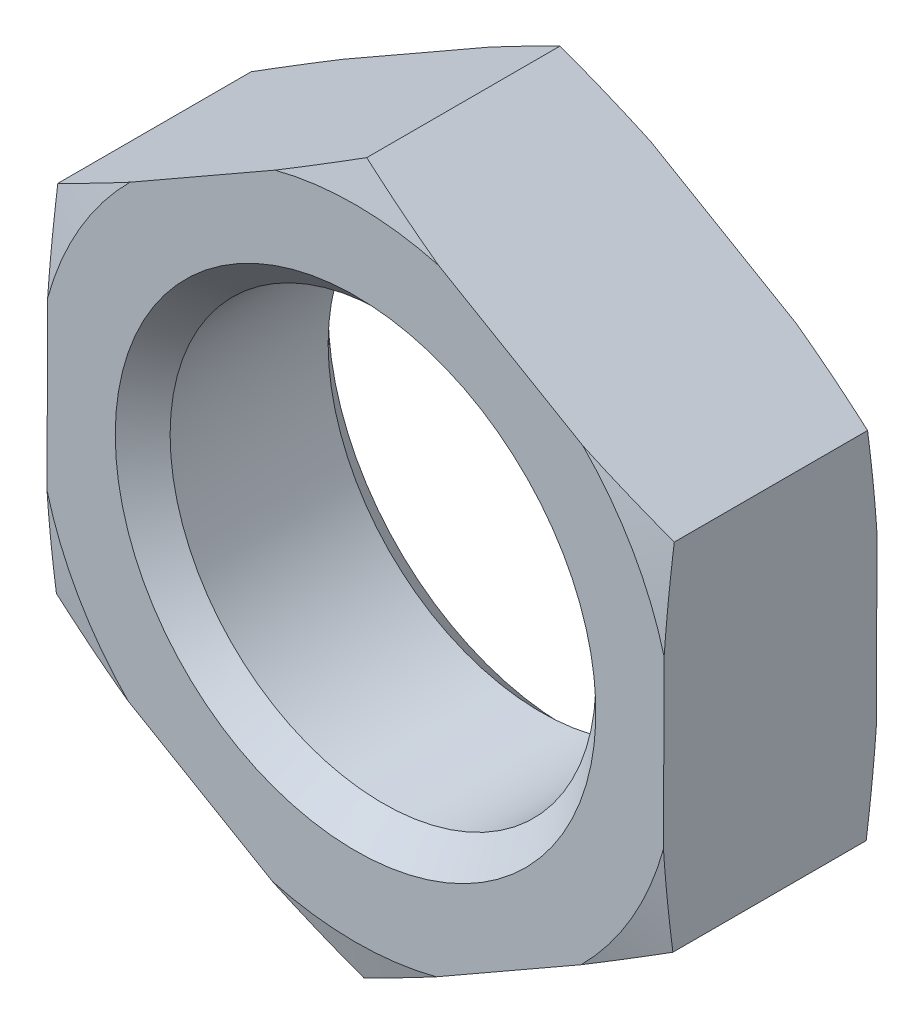
SolidWorks part; units mm, degrees
ref_plane "基准面1" through (0, 0, 0) normal (0, 0, 1) x (1, 0, 0)
ref_plane "基准面2" through (0, 0, 0) normal (0, 1, 0) x (1, 0, 0)
ref_plane "基准面3" through (0, 0, 0) normal (1, 0, 0) x (0, 0, -1)
sketch "尺寸草图" plane through (0, 0, 0) normal (0, 0, 1) x (1, 0, 0)
  line L0 (0, 0) -> (24.1005, 0)
  line L1 (0, 0) -> (17.3, 0)
  line L2 (46.8781, 0) -> (69.3781, 0)
  line L3 (-15.2381, 0) -> (0, 0)
  point P3 (16, 0)
  point P4 (2.5, 0)
  point P5 (26.75, 0)
  point P6 (8, 0)
  point P7 (7.3, 0)
  point P8 (24, 0)
  dimension "D1" = 15.2381
  dimension "D" = 16
  dimension "P" = 2.5
  dimension "e" = 26.75
  dimension "m" = 8
  dimension "mw" = 7.3
  dimension "s" = 24
  dimension "da" = 17.3
  dimension "dw" = 22.5
sketch "草图1" plane through (0, 0, 0) normal (0, 0, 1) x (1, 0, 0)
  line L0 (-26.8088, 0) -> (37.1748, 0) construction
  line L1 (0, 25.0215) -> (0, -25.0215) construction
  line L3 (0.0526, 13.3749) -> (-11.5567, 6.733)
  line L4 (-11.5567, 6.733) -> (-11.6093, -6.6419)
  line L5 (-11.6093, -6.6419) -> (-0.0526, -13.3749)
  line L6 (-0.0526, -13.3749) -> (11.5567, -6.733)
  line L7 (11.5567, -6.733) -> (11.6093, 6.6419)
  line L8 (11.6093, 6.6419) -> (0.0526, 13.3749)
  circle A0 centre (0, 0) radius 11.5831 construction
  circle A1 centre (0, 0) radius 8
  dimension "D" = 16
  dimension "e" = 26.75
extrude "基体-拉伸" add sketch "草图1" along normal blind 8
cosmetic thread "装饰螺纹线1"
chamfer "倒角1" distance 1.031 angle 45 2 edges at (8, 0, 0) (8, 0, 8)
sketch "草图2" plane through (0, 0, 0) normal (0, 0, -1) x (-1, 0, 0)
  circle A0 centre (0, 0) radius 12
  circle A1 centre (0, 0) radius 8 construction
  dimension "s" = 24
extrude "切除-拉伸1" cut sketch "草图2" against normal through all draft 75 flip side to cut
sketch "草图3" plane through (0, 0, 8) normal (0, 0, 1) x (1, 0, 0)
  circle A0 centre (0, 0) radius 12
  dimension "D1" = 24
extrude "切除-拉伸2" cut sketch "草图3" against normal through all draft 75 flip side to cut
equation "\"e@草图1\" = \"e@尺寸草图\""
equation "\"D1@尺寸草图\" = \"D@尺寸草图\" / 1.05"
equation "\"D@草图1\" = \"D@尺寸草图\""
equation "\"m@基体-拉伸\" = \"m@尺寸草图\""
equation "\"D1@草图3\" = \"s@尺寸草图\""
equation "\"s@草图2\" = \"s@尺寸草图\""
equation "\"D2@装饰螺纹线1\" = 1.05 * \"D1@尺寸草图\""
equation "\"D1@倒角1\" =  ( \"da@尺寸草图\" - \"D1@尺寸草图\" )  / 2"
